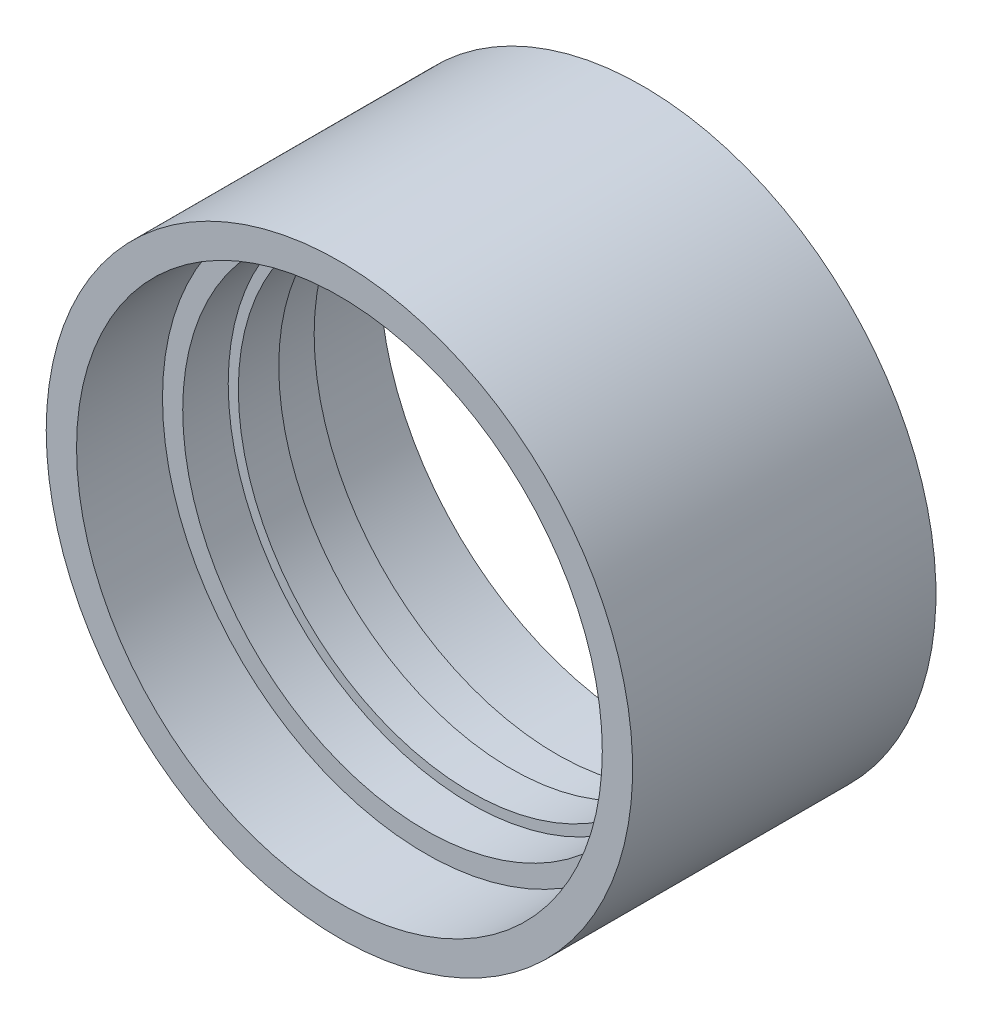
SolidWorks part; units mm, degrees
material "PMMA"
ref_plane "Ebene vorne" through (0, 0, 0) normal (0, 0, 1) x (1, 0, 0)
ref_plane "Ebene oben" through (0, 0, 0) normal (0, 1, 0) x (1, 0, 0)
ref_plane "Ebene rechts" through (0, 0, 0) normal (1, 0, 0) x (0, 0, -1)
sketch "Skizze1" plane through (0, 0, 0) normal (1, 0, 0) x (0, 0, -1)
  line L0 (-15, 29) -> (15, 29)
  line L1 (15, 29) -> (15, 26)
  line L2 (15, 26) -> (6.5, 26)
  line L3 (-6.5, 26) -> (-6.5, 24)
  line L4 (2, 23) -> (-2, 23)
  line L5 (-6.5, 24) -> (-2, 24)
  line L6 (-6.5, 26) -> (-15, 26)
  line L7 (-15, 26) -> (-15, 29)
  line L8 (12.1292, 0) -> (-15.875, 0) construction
  line L9 (0, 23) -> (0, 0) construction
  line L10 (0, 23) -> (0, 29) construction
  line L11 (-2, 24) -> (-2, 23)
  line L12 (2, 23) -> (2, 24)
  line L13 (2, 24) -> (6.5, 24)
  line L14 (6.5, 24) -> (6.5, 26)
  dimension "D1" = 52
  dimension "D2" = 46
  dimension "D3" = 8.5
  dimension "D4" = 13
  dimension "D5" = 3
  dimension "D6" = 4
  dimension "D7" = 48
revolve "Rotation1" add sketch "Skizze1" angle 360 about L8
